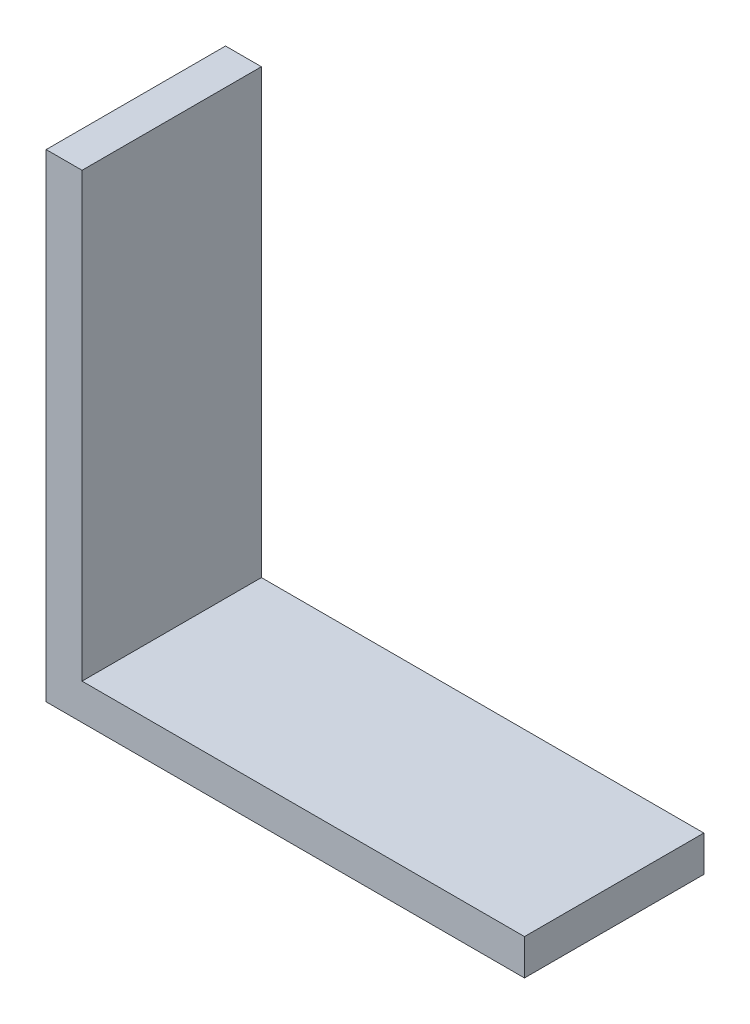
SolidWorks part; units mm, degrees
ref_plane "Front Plane" through (0, 0, 0) normal (0, 0, 1) x (1, 0, 0)
ref_plane "Top Plane" through (0, 0, 0) normal (0, 1, 0) x (1, 0, 0)
ref_plane "Right Plane" through (0, 0, 0) normal (1, 0, 0) x (0, 0, -1)
sketch "Sketch1" plane through (0, 0, 0) normal (0, 1, 0) x (1, 0, 0)
  line L1 (0, 0) -> (40, 0)
  line L2 (0, 0) -> (0, 15)
  line L3 (0, 15) -> (40, 15)
  line L4 (40, 0) -> (40, 15)
  dimension "D1" = 15
  dimension "D2" = 40
extrude "Boss-Extrude1" add sketch "Sketch1" along normal blind 3
sketch "Sketch2" plane through (0, 3, 0) normal (0, 1, 0) x (1, 0, 0)
  line L0 (40, 15) -> (0, 15) construction
  line L1 (0, 0) -> (3, 0)
  line L2 (0, 0) -> (0, 15)
  line L3 (0, 15) -> (3, 15)
  line L4 (3, 0) -> (3, 15)
  dimension "D1" = 3
extrude "Boss-Extrude2" add sketch "Sketch2" along normal blind 37
